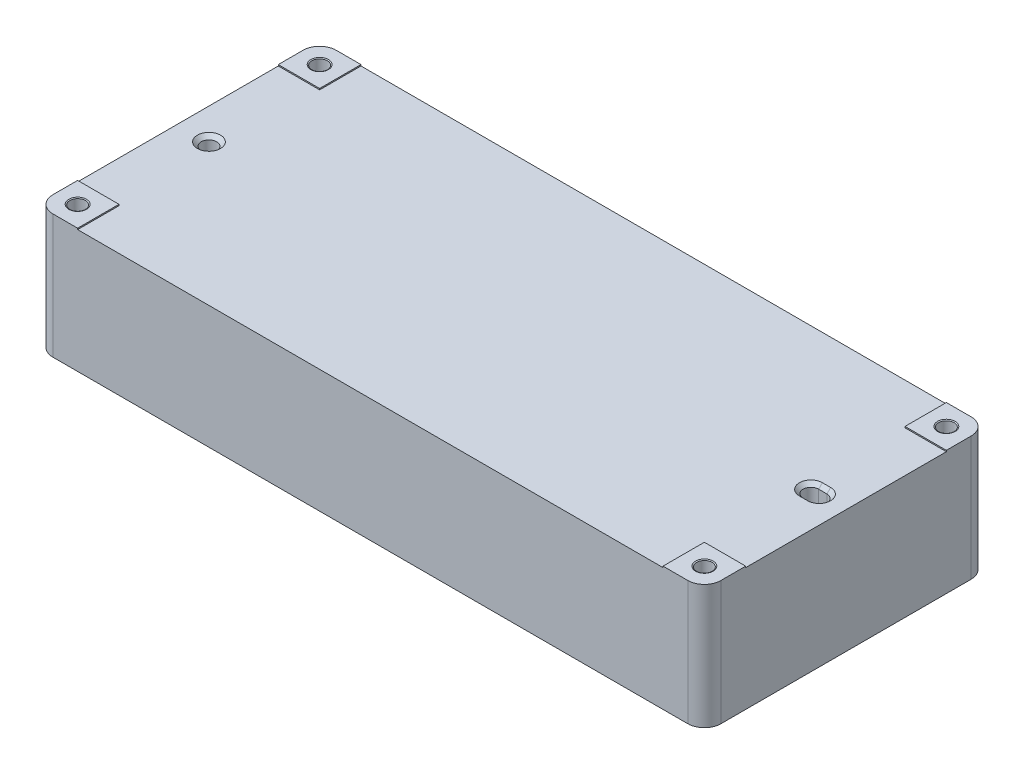
SolidWorks part; units mm, degrees
material "6061-T6 Al"
ref_plane "Front" through (0, 0, 0) normal (0, 0, 1) x (1, 0, 0)
ref_plane "Top" through (0, 0, 0) normal (0, 1, 0) x (1, 0, 0)
ref_plane "Right" through (0, 0, 0) normal (1, 0, 0) x (0, 0, -1)
sketch "Sketch1" plane through (0, 0, 0) normal (0, 1, 0) x (1, 0, 0)
  line L0 (0, 0) -> (0, 86.995) construction
  line L1 (-205.105, 86.995) -> (205.105, 86.995)
  line L2 (-205.105, 86.995) -> (-205.105, -86.995)
  line L3 (-205.105, -86.995) -> (205.105, -86.995)
  line L4 (205.105, 86.995) -> (205.105, -86.995)
  line L5 (0, 0) -> (205.105, 0) construction
  dimension "D1" = 410.21
  dimension "D2" = 173.99
extrude "Extrude1" add sketch "Sketch1" along normal mid plane 76.2
sketch "Sketch2" plane through (0, 38.1, 0) normal (0, 1, 0) x (1, 0, 0)
  line L0 (-205.105, 61.595) -> (-179.705, 61.595)
  line L1 (-205.105, 86.995) -> (-205.105, -86.995) construction
  line L2 (-179.705, 61.595) -> (-179.705, 86.995)
  line L3 (205.105, 86.995) -> (-205.105, 86.995) construction
  line L4 (-179.705, 86.995) -> (179.705, 86.995)
  line L5 (179.705, 86.995) -> (179.705, 61.595)
  line L6 (179.705, 61.595) -> (205.105, 61.595)
  line L7 (205.105, -86.995) -> (205.105, 86.995) construction
  line L8 (205.105, 61.595) -> (205.105, -61.595)
  line L9 (205.105, -61.595) -> (179.705, -61.595)
  line L10 (179.705, -61.595) -> (179.705, -86.995)
  line L11 (-205.105, -86.995) -> (205.105, -86.995) construction
  line L12 (179.705, -86.995) -> (-179.705, -86.995)
  line L13 (-179.705, -86.995) -> (-179.705, -61.595)
  line L14 (-179.705, -61.595) -> (-205.105, -61.595)
  line L15 (-205.105, -61.595) -> (-205.105, 61.595)
  dimension "D1" = 25.4
  dimension "D2" = 25.4
  dimension "D3" = 25.4
  dimension "D4" = 25.4
  dimension "D5" = 25.4
  dimension "D6" = 25.4
  dimension "D7" = 25.4
  dimension "D8" = 25.4
extrude "Extrude2" cut sketch "Sketch2" against normal blind 0.762
hole_wizard "3/8-16 Tapped Hole2" positions "Sketch4" profile "Sketch3" tap size "3/8-16" standard "Ansi Inch" end condition through all
sketch "Sketch4" plane through (0, 38.1, 0) normal (0, 1, 0) x (-1, 0, 0)
  line L0 (205.105, -86.995) -> (205.105, -61.595) construction
  line L1 (179.705, -86.995) -> (205.105, -86.995) construction
  line L3 (205.105, 61.595) -> (205.105, 86.995) construction
  line L4 (205.105, 86.995) -> (179.705, 86.995) construction
  line L5 (-179.705, 86.995) -> (-205.105, 86.995) construction
  line L6 (-205.105, 86.995) -> (-205.105, 61.595) construction
  line L7 (-205.105, -61.595) -> (-179.705, -61.595) construction
  line L8 (-179.705, -61.595) -> (-179.705, -86.995) construction
  point P0 (192.405, -74.295)
  point P1 (192.405, 74.295)
  point P3 (-192.405, 74.295)
  point P5 (-192.405, -74.295)
  point P25 (-179.705, -74.295)
  dimension "D1" = 12.7
  dimension "D2" = 12.7
  dimension "D3" = 12.7
  dimension "D4" = 12.7
  dimension "D5" = 12.7
  dimension "D6" = 12.7
  dimension "D7" = 12.7
  dimension "D8" = 12.7
sketch "Sketch3" plane through (-192.405, 38.1, -74.295) normal (1, 0, 0) x (0, 0, 1)
  line L0 (0, 0) -> (0, 76.2)
  line L1 (0, 76.2) -> (3.9687, 76.2)
  line L3 (3.9687, 76.2) -> (3.9688, 25.4)
  line L4 (4.7625, 25.4) -> (3.9688, 25.4)
  line L5 (4.7625, 25.4) -> (4.7625, 0.3666)
  line L6 (4.7625, 0.3666) -> (5.3975, 0)
  line L7 (5.3975, 0) -> (0, 0)
  line L8 (-4.7625, 0.3666) -> (-5.3975, 0) construction
  line L11 (0, -6.35) -> (0, 107.95) construction
  dimension "Thru Tap Drill Dia." = 7.9375
  dimension "Thru Tap Drill Depth" = 76.2
  dimension "Thread Major Dia." = 9.525
  dimension "Thread Depth" = 25.4
  dimension "Near C'Sink Dia." = 10.795
  dimension "Near C'Sink Angle" = 120
fillet "Fillet1" radius 10.16 4 edges at (205.105, 0, 86.995) (205.105, 0, -86.995) (-205.105, 0, -86.995) (-205.105, 0, 86.995)
hole_wizard "3/8 dowel pin hole" positions "Sketch6" profile "Sketch5" hole size "3/8" standard "Ansi Inch"
sketch "Sketch6" plane through (0, 37.338, 0) normal (0, 1, 0) x (-1, 0, 0)
  line L0 (205.105, 0) -> (-205.105, 0) construction
  line L1 (205.105, -61.595) -> (205.105, 61.595) construction
  line L2 (-205.105, 61.595) -> (-205.105, -61.595) construction
  point P0 (186.055, 0)
  dimension "D1" = 19.05
sketch "Sketch5" plane through (-186.055, 37.338, 0) normal (1, 0, 0) x (0, 0, 1)
  line L0 (0, 0) -> (0, 23.8214)
  line L1 (0, 23.8214) -> (4.7714, 19.05)
  line L2 (4.7714, 19.05) -> (4.7714, 2.3406)
  line L3 (4.7714, 2.3406) -> (7.112, 0)
  line L5 (7.112, 0) -> (0, 0)
  line L6 (-4.7714, 2.3406) -> (-7.112, 0) construction
  line L10 (0, 23.8214) -> (-4.7714, 19.05) construction
  line L11 (0, -6.35) -> (0, 107.95) construction
  dimension "Hole Dia." = 9.5428
  dimension "Hole Depth" = 19.05
  dimension "Near C'Sink Dia." = 14.224
  dimension "Near C'Sink Angle" = 90
  dimension "Drill Angle" = 90
sketch "Sketch7" plane through (0, 37.338, 0) normal (0, 1, 0) x (1, 0, 0)
  line L0 (-205.105, 0) -> (205.105, 0) construction
  line L1 (-205.105, 61.595) -> (-205.105, -61.595) construction
  line L2 (205.105, -61.595) -> (205.105, 61.595) construction
  line L3 (183.515, 0) -> (188.595, 0) construction
  line L4 (183.515, 4.7714) -> (188.595, 4.7714)
  line L5 (183.515, -4.7714) -> (188.595, -4.7714)
  arc A0 (183.515, 4.7714) -> (183.515, -4.7714) centre (183.515, 0) ccw
  arc A1 (188.595, -4.7714) -> (188.595, 4.7714) centre (188.595, 0) ccw
  point P8 (186.055, 0)
  dimension "D3" = 4.7714
  dimension "D1" = 19.05
  dimension "D2" = 5.08
extrude "Extrude3" cut sketch "Sketch7" against normal blind 19.05
chamfer "Chamfer1" distance 2.286 angle 45 4 edges at (186.055, 37.338, 4.7714) (193.3664, 37.338, 0) (178.7436, 37.338, 0) (186.055, 37.338, -4.7714)
hole_wizard "7/32 (0.21875) Diameter Hole Vented Holes" positions "Sketch16" profile "Sketch15" hole size "9/32" standard "Ansi Inch" end condition through all
sketch "Sketch16" plane through (0, 37.338, 0) normal (0, 1, 0) x (-1, 0, 0)
  line L3 (-186.055, 0) -> (-186.055, 4.7714) construction
  line L4 (-183.515, 4.7714) -> (-188.595, 4.7714) construction
  line L6 (-186.055, 0) -> (-193.3664, 0) construction
  arc A0 (-188.595, 4.7714) -> (-188.595, -4.7714) centre (-188.595, 0) ccw construction
  point P0 (-186.055, 0)
  point P27 (186.055, 0)
sketch "Sketch15" plane through (186.055, 37.338, 0) normal (1, 0, 0) x (0, 0, 1)
  line L0 (0, 0) -> (0, 75.438)
  line L1 (0, 75.438) -> (3.5719, 75.438)
  line L2 (3.5719, 75.438) -> (3.5719, 0)
  line L5 (3.5719, 0) -> (0, 0)
  line L11 (0, -6.35) -> (0, 107.95) construction
  dimension "Thru Hole Dia." = 7.1437
  dimension "Thru Hole Depth" = 75.438
